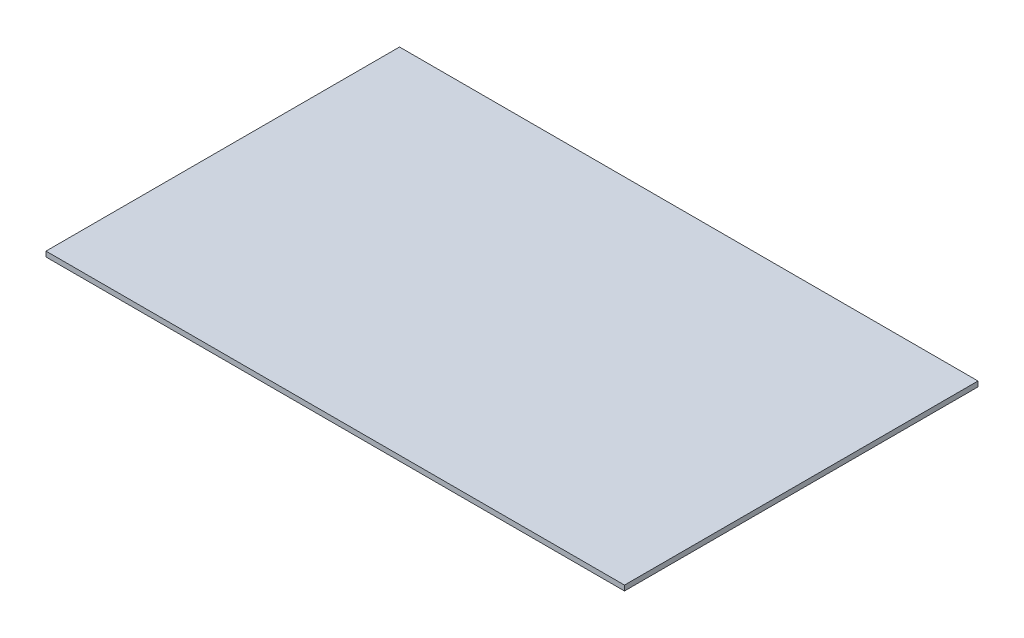
SolidWorks part; units mm, degrees
ref_plane "Front Plane" through (0, 0, 0) normal (0, 0, 1) x (1, 0, 0)
ref_plane "Top Plane" through (0, 0, 0) normal (0, 1, 0) x (1, 0, 0)
ref_plane "Right Plane" through (0, 0, 0) normal (1, 0, 0) x (0, 0, -1)
sketch "Sketch1" plane through (0, 0, 0) normal (0, 1, 0) x (1, 0, 0)
  line L0 (0, 88.3663) -> (0, -91.6337) construction
  line L1 (-104.5545, 0) -> (111.6832, 0) construction
  line L2 (-90, -55) -> (-90, 55)
  line L3 (-90, 55) -> (90, 55)
  line L4 (90, -55) -> (90, 55)
  line L5 (-90, -55) -> (90, -55)
  point P5 (0, -55)
  point P9 (0, 55)
  point P11 (90, 0)
  point P12 (-90, 0)
  dimension "D1" = 180
  dimension "D2" = 110
extrude "Boss-Extrude1" add sketch "Sketch1" along normal blind 1.6
